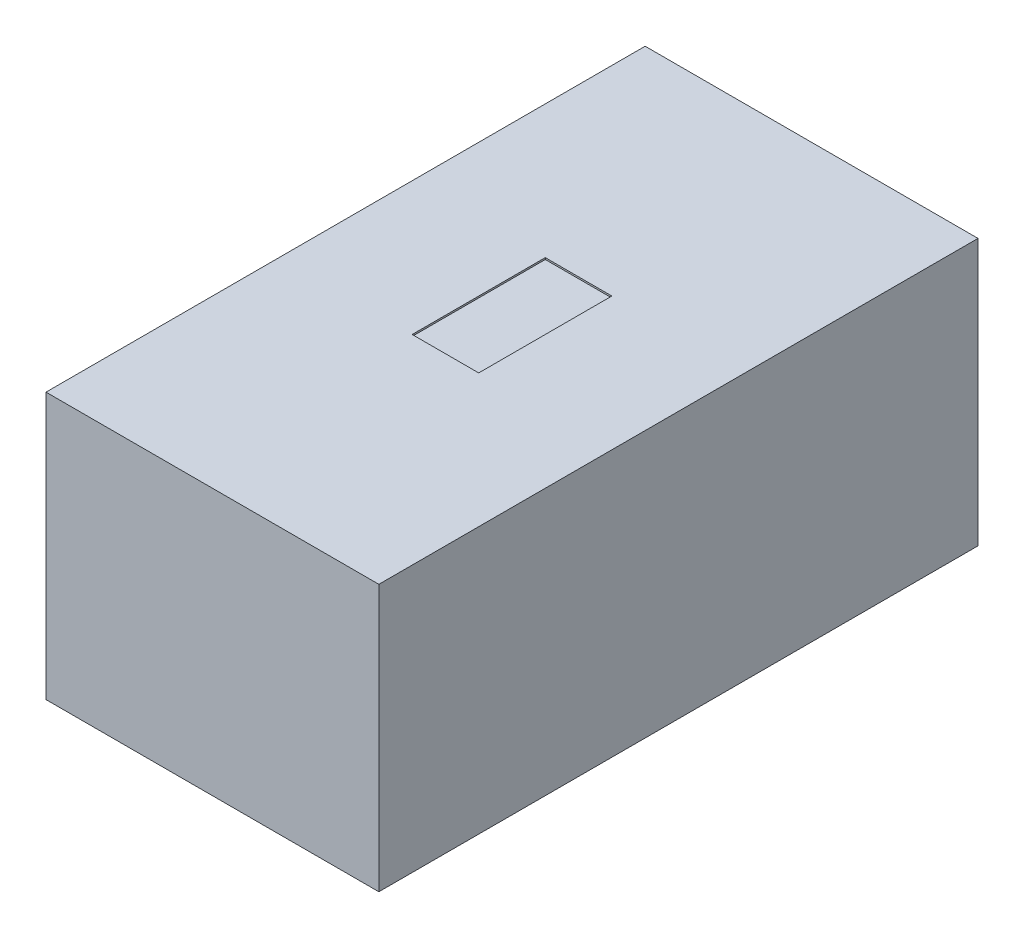
SolidWorks part; units mm, degrees
ref_plane "Front Plane" through (0, 0, 0) normal (0, 0, 1) x (1, 0, 0)
ref_plane "Top Plane" through (0, 0, 0) normal (0, 1, 0) x (1, 0, 0)
ref_plane "Right Plane" through (0, 0, 0) normal (1, 0, 0) x (0, 0, -1)
sketch "ProfileS" plane through (0, 0, 0) normal (0, 1, 0) x (1, 0, 0)
  line L1 (-0.5, 0.9) -> (0.5, 0.9)
  line L2 (-0.5, 0.9) -> (-0.5, -0.9)
  line L3 (-0.5, -0.9) -> (0.5, -0.9)
  line L4 (0.5, 0.9) -> (0.5, -0.9)
  line L5 (-0.5, 0.9) -> (0.5, -0.9) construction
  line L6 (-0.5, -0.9) -> (0.5, 0.9) construction
  point P0 (0, 0)
  dimension "Width" = 1
  dimension "Length" = 1.8
extrude "Profile" add sketch "ProfileS" along normal blind 0.8
sketch "TopCutS" plane through (0, 0.8, 0) normal (0, 1, 0) x (1, 0, 0)
  line L1 (-0.1, 0.2) -> (0.1, 0.2)
  line L2 (-0.1, 0.2) -> (-0.1, -0.2)
  line L3 (-0.1, -0.2) -> (0.1, -0.2)
  line L4 (0.1, 0.2) -> (0.1, -0.2)
  line L5 (-0.1, 0.2) -> (0.1, -0.2) construction
  line L6 (-0.1, -0.2) -> (0.1, 0.2) construction
  point P0 (0, 0)
  dimension "Width" = 0.2
  dimension "Length" = 0.4
extrude "TopCut" cut sketch "TopCutS" against normal blind 0.005
